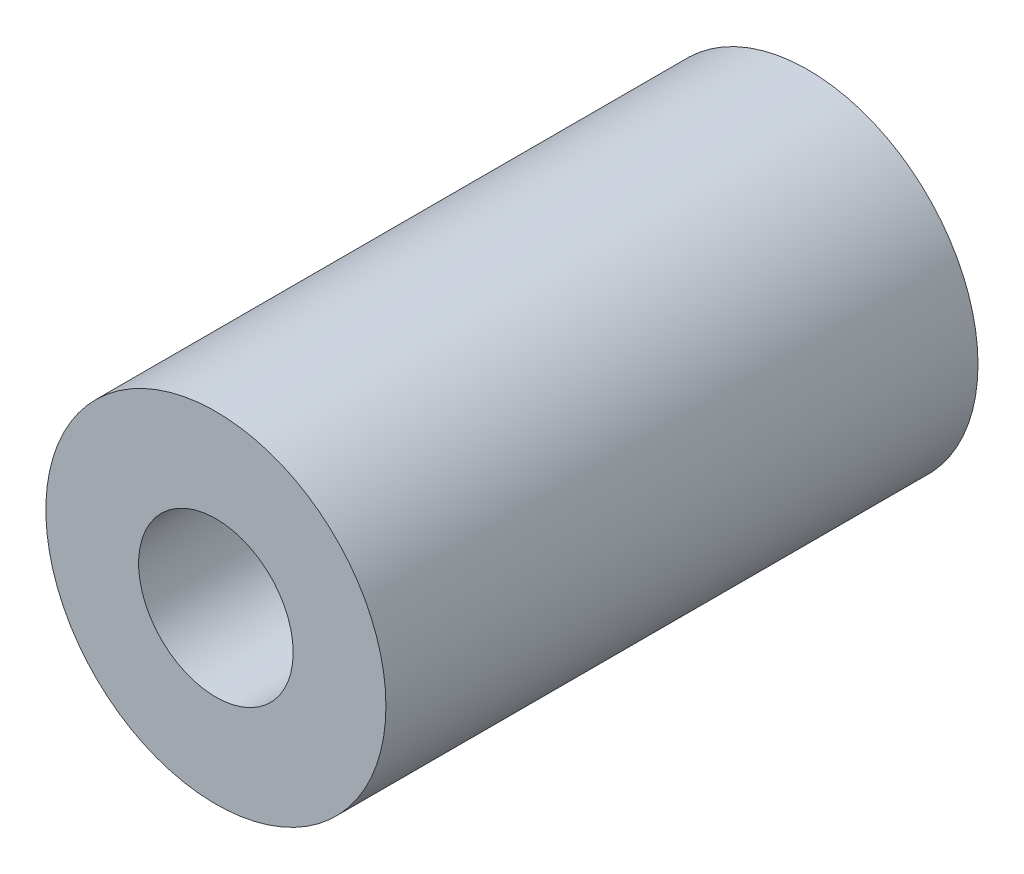
SolidWorks part; units mm, degrees
ref_plane "Front Plane" through (0, 0, 0) normal (0, 0, 1) x (1, 0, 0)
ref_plane "Top Plane" through (0, 0, 0) normal (0, 1, 0) x (1, 0, 0)
ref_plane "Right Plane" through (0, 0, 0) normal (1, 0, 0) x (0, 0, -1)
sketch "Sketch1" plane through (0, 0, 0) normal (0, 0, 1) x (1, 0, 0)
  circle A0 centre (0, 0) radius 2.5
  circle A1 centre (0, 0) radius 5.5
  dimension "D1" = 11
  dimension "D2" = 5
extrude "Boss-Extrude1" add sketch "Sketch1" along normal blind 19.15
